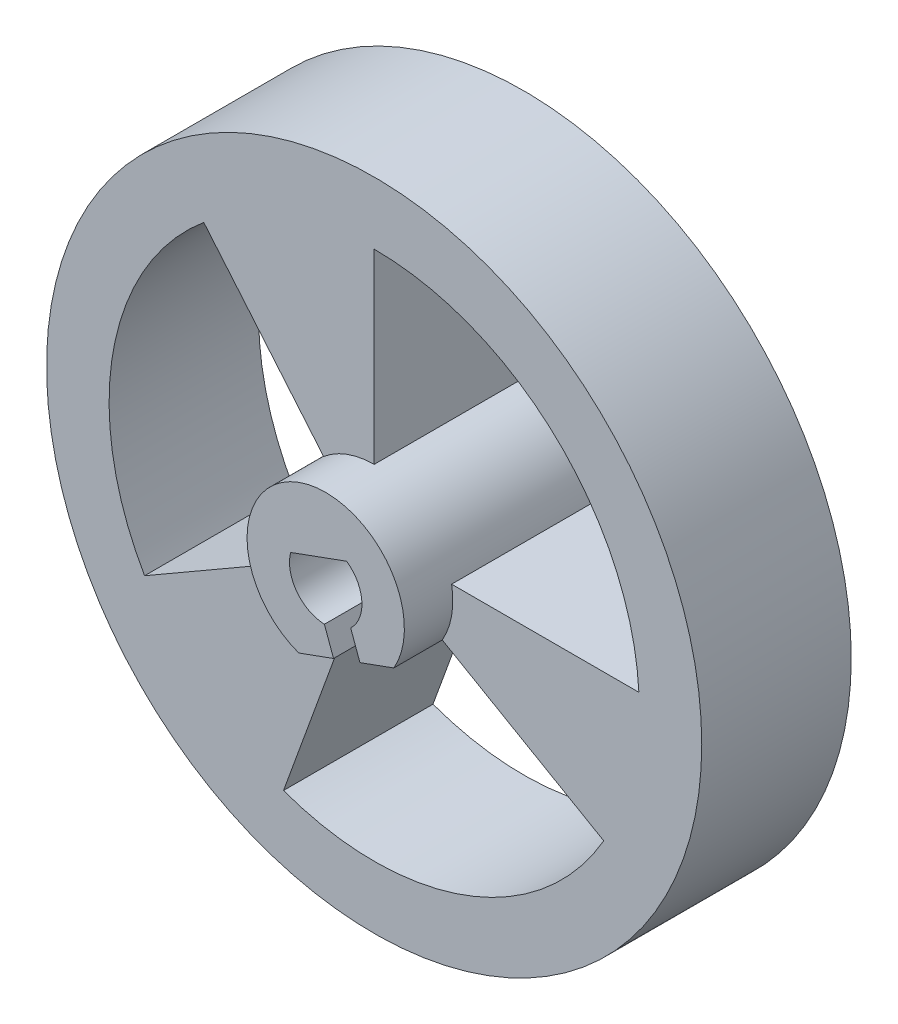
SolidWorks part; units mm, degrees
ref_plane "Plan de face" through (0, 0, 0) normal (0, 0, 1) x (1, 0, 0)
ref_plane "Plan de dessus" through (0, 0, 0) normal (0, 1, 0) x (1, 0, 0)
ref_plane "Plan de droite" through (0, 0, 0) normal (1, 0, 0) x (0, 0, -1)
sketch "Esquisse2" plane through (0, 0, 0) normal (0, 0, 1) x (1, 0, 0)
  line L0 (0, 11.49) -> (0, 3.41)
  line L1 (2.9531, -1.705) -> (-1.1663, -3.2044) construction
  line L3 (3.3582, 0.5921) -> (11.4747, 0.5921)
  line L4 (2.9531, -1.705) -> (9.9506, -5.745)
  line L5 (-2.1919, 2.6122) -> (-7.3856, 8.8019)
  line L6 (-2.9531, -1.705) -> (-9.9506, -5.745)
  line L7 (-1.1663, -3.2044) -> (-3.9298, -10.7971)
  line L8 (-1.5195, 0.3951) -> (0.91, 1.2794)
  line L11 (-0.0174, -1.6771) -> (-0.0568, -1.569)
  line L12 (-0.0174, -1.6771) -> (0.5943, -3.3578)
  line L13 (1.127, -1.2606) -> (1.7363, -2.9348)
  line L14 (1.127, -1.2606) -> (1.0822, -1.1375)
  arc A0 (0.5943, -3.3578) -> (-1.1663, -3.2044) centre (0, 0) cw
  circle A1 centre (0, 0) radius 14.2
  arc A2 (-7.3856, 8.8019) -> (-9.9506, -5.745) centre (0, 0) ccw
  arc A3 (-2.1919, 2.6122) -> (-2.9531, -1.705) centre (0, 0) ccw
  arc A4 (0, 3.41) -> (3.3582, 0.5921) centre (0, 0) cw
  arc A5 (2.9531, -1.705) -> (1.7363, -2.9348) centre (0, 0) cw
  arc A6 (2.9531, -1.705) -> (1.7363, -2.9348) centre (0, 0) cw
  arc A7 (3.3582, 0.5921) -> (0, 3.41) centre (0, 0) ccw
  arc A8 (0, 3.41) -> (3.3582, 0.5921) centre (0, 0) cw
  arc A9 (-2.1919, 2.6122) -> (-2.9531, -1.705) centre (0, 0) ccw
  arc A10 (11.4747, 0.5921) -> (0, 11.49) centre (0, 0) ccw
  arc A11 (-1.1663, -3.2044) -> (0.5943, -3.3578) centre (0, 0) ccw
  arc A12 (-2.9531, -1.705) -> (-3.3582, 0.5921) centre (0, 0) cw
  arc A13 (-3.9298, -10.7971) -> (9.9506, -5.745) centre (0, 0) ccw
  arc A14 (-1.5195, 0.3951) -> (-0.0568, -1.569) centre (0, 0) ccw
  arc A15 (1.7363, -2.9348) -> (2.9531, -1.705) centre (0, 0) ccw
  arc A16 (1.0822, -1.1375) -> (0.91, 1.2794) centre (0, 0) ccw
  point P8 (0, 3.41)
  dimension "D1" = 28.4
  dimension "D2" = 1.57
  dimension "D4" = 2.71
extrude "Boss.-Extru.8" add sketch "Esquisse2" along normal blind 6.48 contours A1 L1 L4 A13 L7 L12 L11 A14 L8 A16 L14 L13 A10 L3 A4 L0 L5 A3 A9 L6 A2
sketch "Esquisse6" plane through (0, 0, 6.48) normal (0, 0, 1) x (1, 0, 0)
  line L0 (-1.5195, 0.3951) -> (0.91, 1.2794)
  line L1 (-0.0568, -1.569) -> (1.0822, -1.1375) construction
  line L2 (-0.0568, -1.569) -> (0.339, -2.6565)
  line L3 (0.339, -2.6565) -> (-1.1663, -3.2044)
  line L4 (1.0822, -1.1375) -> (1.4834, -2.2399)
  line L5 (1.4834, -2.2399) -> (2.9531, -1.705)
  line L6 (-1.1663, -3.2044) -> (2.9531, -1.705) construction
  arc A0 (-1.5195, 0.3951) -> (-0.0568, -1.569) centre (0, 0) ccw
  arc A1 (2.9531, -1.705) -> (-1.1663, -3.2044) centre (0, 0) ccw
  arc A2 (1.0822, -1.1375) -> (0.91, 1.2794) centre (0, 0) ccw
extrude "Boss.-Extru.9" add sketch "Esquisse6" along normal blind 2.1
